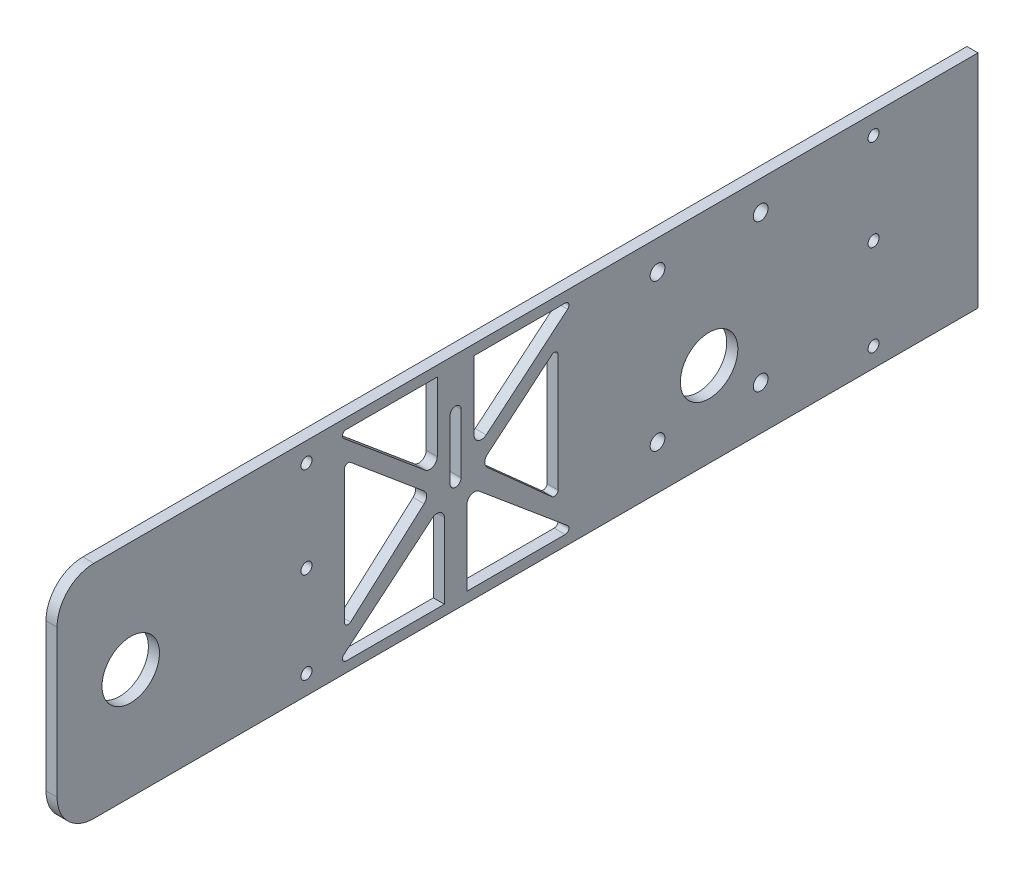
SolidWorks part; units mm, degrees
material "6061 Alloy"
ref_plane "Front Plane" through (0, 0, 0) normal (0, 0, 1) x (1, 0, 0)
ref_plane "Top Plane" through (0, 0, 0) normal (0, 1, 0) x (1, 0, 0)
ref_plane "Right Plane" through (0, 0, 0) normal (1, 0, 0) x (0, 0, -1)
sketch "Sketch1" plane through (0, 0, 0) normal (0, 0, 1) x (1, 0, 0)
  line L1 (1.5, -30) -> (-1.5, -30)
  line L2 (1.5, -30) -> (1.5, 30)
  line L3 (1.5, 30) -> (-1.5, 30)
  line L4 (-1.5, -30) -> (-1.5, 30)
  line L5 (1.5, -30) -> (-1.5, 30) construction
  line L6 (1.5, 30) -> (-1.5, -30) construction
  point P0 (0, 0)
  dimension "D1" = 60
  dimension "D2" = 3
extrude "Boss-Extrude1" add sketch "Sketch1" along normal blind 250
fillet "Fillet1" radius 10 1 edges at (0, 30, 250)
fillet "Fillet2" radius 10 1 edges at (0, -30, 250)
sketch "Sketch2" plane through (-1.5, 0, 0) normal (-1, 0, 0) x (0, 0, 1)
  line L0 (250, 0) -> (230, 0)
  line L1 (250, 20) -> (250, -20) construction
  circle A0 centre (230, 0) radius 4.25
extrude "Cut-Extrude1" cut sketch "Sketch2" against normal through all
sketch "Sketch3" plane through (1.5, 0, 0) normal (1, 0, 0) x (0, 0, -1)
  circle A0 centre (-10.5, 12.5) radius 2
  circle A1 centre (-10.5, 0) radius 2
  circle A2 centre (-10.5, -12.5) radius 2
sketch "Sketch9" plane through (1.5, 0, 0) normal (1, 0, 0) x (0, 0, -1)
  circle A0 centre (-230, 0) radius 7.8
extrude "Cut-Extrude7" cut sketch "Sketch9" against normal through all
sketch "Sketch11" plane through (-1.5, 0, 0) normal (-1, 0, 0) x (0, 0, 1)
  line L0 (0, -30) -> (0, -7) construction
  line L1 (0, -7) -> (73, -7) construction
  circle A0 centre (73, -7) radius 7.8
extrude "Cut-Extrude8" cut sketch "Sketch11" against normal through all
sketch "Sketch13" plane through (1.5, 0, 0) normal (1, 0, 0) x (0, 0, -1)
  circle A0 centre (-87, 22) radius 2
  circle A1 centre (-59, 22) radius 2
  circle A2 centre (-59, -18) radius 2
  circle A3 centre (-87, -18) radius 2
  dimension "D1" = 4
extrude "Cut-Extrude9" cut sketch "Sketch13" against normal through all
sketch "Sketch16" plane through (1.5, 0, 0) normal (1, 0, 0) x (0, 0, -1)
  line L0 (-240, 30) -> (0, 30) construction
  line L1 (-174.2886, 27.2) -> (-109.2886, 27.2)
  line L2 (-174.2886, 27.2) -> (-174.2886, -27.2)
  line L3 (-174.2886, -27.2) -> (-109.2886, -27.2)
  line L4 (-109.2886, 27.2) -> (-109.2886, -27.2)
  line L5 (-240, -30) -> (0, -30) construction
  line L6 (-179.2886, 30) -> (-179.2886, -30) construction
  line L7 (-174.2886, 27.2) -> (-141.7886, 0)
  line L8 (-141.7886, 0) -> (-174.2886, -27.2)
  line L9 (-174.2886, 22.2) -> (-148.6172, 0.715)
  line L10 (-148.6172, 0.715) -> (-174.2886, -22.2)
  line L11 (-141.7886, -27.2) -> (-141.7886, 27.2)
  line L12 (-141.7886, 0) -> (-109.2886, -27.2)
  line L13 (-134.96, 0.715) -> (-109.2886, -22.2)
  line L14 (-109.2886, 27.2) -> (-141.7886, 0)
  line L15 (-109.2886, 22.2) -> (-134.96, 0.715)
  line L16 (-171.9818, 20.2694) -> (-171.9818, -20.1409)
  line L17 (-114, 18.2569) -> (-114, -17.9944)
  line L18 (-114, -22.5) -> (-114, 8.5) construction
  line L19 (-144.856, -2.5672) -> (-138.7211, -2.5672) construction
  line L24 (-146.7886, 4.1846) -> (-136.7886, 4.1846) construction
  line L25 (-144.856, -2.5672) -> (-144.856, -27.2)
  line L26 (-138.7211, -2.5672) -> (-138.7211, -27.2)
  line L27 (-136.7886, 4.1846) -> (-136.7886, 27.2)
  line L28 (-146.7886, 4.1846) -> (-146.7886, 27.2)
  point P10 (-141.7886, -27.2)
  point P12 (-109.2886, 0)
  point P20 (-141.7886, 0)
  dimension "D1" = 2.8
  dimension "D2" = 2.8
  dimension "D3" = 5
  dimension "D4" = 65
  dimension "D5" = 5
  dimension "D6" = 5
  dimension "D7" = 4
  dimension "D8" = 10
extrude "Cut-Extrude13" cut sketch "Sketch16" against normal blind 10 contours L7 L28 L1 | L27 L14 L1 | L17 L15 L13 | L9 L16 L10 | L12 L26 L3 | L25 L8 L3
fillet "Fillet3" radius 2 6 edges at (0, -2.5672, 138.7211) (0, -2.5672, 144.856) (0, 0.715, 148.6172) (0, 4.1846, 146.7886) (0, 4.1846, 136.7886) (0, 0.715, 134.96)
fillet "Fillet4" radius 1 8 edges at (0, -20.1409, 171.9818) (0, 20.2694, 171.9818) (0, 27.2, 174.2886) (0, -27.2, 174.2886) (0, -27.2, 109.2886) (0, -17.9944, 114) (0, 27.2, 109.2886) (0, 18.2569, 114)
sketch "Sketch17" plane through (-1.5, 0, 0) normal (-1, 0, 0) x (0, 0, 1)
  line L0 (143.3153, 0.2905) -> (143.3153, 16.3836) construction
  line L1 (141.8153, 0.2905) -> (141.8153, 16.3836)
  line L2 (144.8153, 0.2905) -> (144.8153, 16.3836)
  line L3 (144.8153, 16.3836) -> (144.8153, 0.2905) construction
  arc A0 (141.8153, 0.2905) -> (144.8153, 0.2905) centre (143.3153, 0.2905) ccw
  arc A1 (144.8153, 16.3836) -> (141.8153, 16.3836) centre (143.3153, 16.3836) ccw
  point P4 (143.3153, 8.337)
  dimension "D1" = 3
sketch "Sketch18" plane through (-1.5, 0, 0) normal (-1, 0, 0) x (0, 0, 1)
  circle A0 centre (182.2886, 24.75) radius 1.5
  circle A1 centre (182.2886, 0) radius 1.5
  circle A2 centre (182.2886, -24.75) radius 1.5
  circle A3 centre (28.3518, 24.75) radius 1.5
  circle A4 centre (28.3518, 0) radius 1.5
  circle A5 centre (28.3518, -24.75) radius 1.5
extrude "Cut-Extrude15" cut sketch "Sketch18" against normal through all
sketch "Sketch22" plane through (1.5, 0, 0) normal (1, 0, 0) x (0, 0, -1)
  line L0 (-144.8153, 16.3836) -> (-136.7886, 16.3836)
  line L1 (-144.8153, 0.2905) -> (-144.8153, 16.3836) construction
  line L2 (-136.7886, 8.4665) -> (-136.7886, 27.2) construction
  line L3 (-144.8153, 0.2905) -> (-141.8153, 0.2905)
  line L4 (-141.8153, 16.3836) -> (-141.8153, 0.2905) construction
  line L5 (-140.3153, 16.3836) -> (-140.3153, 0.2905)
  line L6 (-143.3153, 16.3836) -> (-143.3153, 0.2905)
  arc A0 (-141.8153, 16.3836) -> (-144.8153, 16.3836) centre (-143.3153, 16.3836) ccw construction
  arc A1 (-140.3153, 16.3836) -> (-143.3153, 16.3836) centre (-141.8153, 16.3836) ccw
  arc A2 (-143.3153, 0.2905) -> (-140.3153, 0.2905) centre (-141.8153, 0.2905) ccw
  point P14 (-141.8153, 8.337)
  dimension "D1" = 1.5
extrude "Cut-Extrude16" cut sketch "Sketch22" against normal through all contours L0 L4 L3 A2 L5 | L4 L0 L6 L3 | L0 A1
